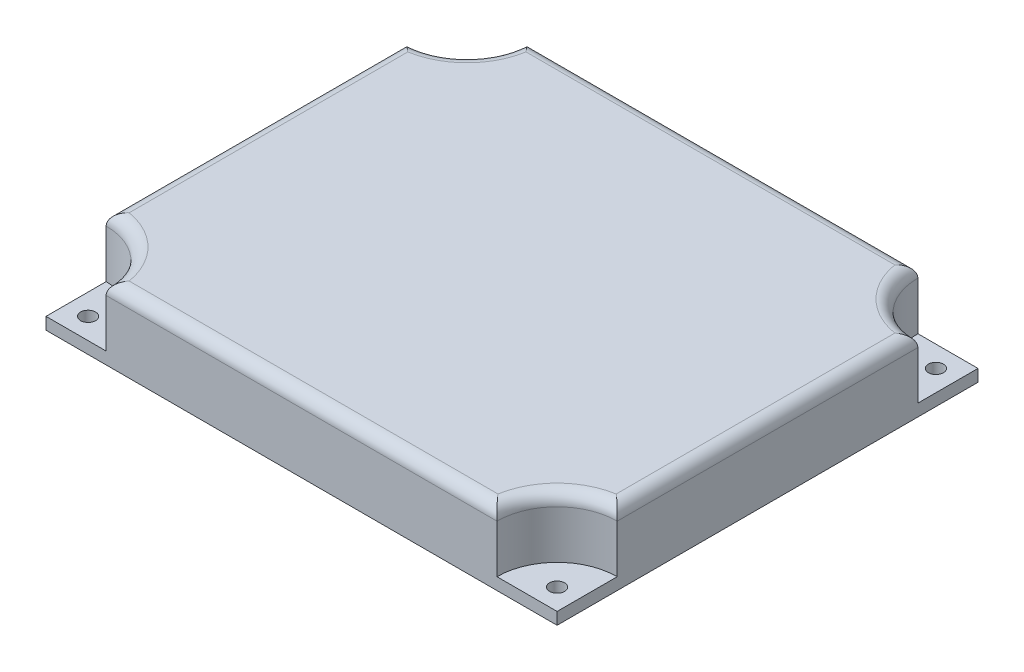
SolidWorks part; units mm, degrees
material "6061-T6 (SS)"
ref_plane "Front Plane" through (0, 0, 0) normal (0, 0, 1) x (1, 0, 0)
ref_plane "Top Plane" through (0, 0, 0) normal (0, 1, 0) x (1, 0, 0)
ref_plane "Right Plane" through (0, 0, 0) normal (1, 0, 0) x (0, 0, -1)
sketch "Sketch2" plane through (0, 0, 0) normal (0, 1, 0) x (1, 0, 0)
  line L1 (-42.5, -35) -> (42.5, -35)
  line L2 (-42.5, -35) -> (-42.5, 35)
  line L3 (-42.5, 35) -> (42.5, 35)
  line L4 (42.5, -35) -> (42.5, 35)
  line L5 (-42.5, -35) -> (42.5, 35) construction
  line L6 (-42.5, 35) -> (42.5, -35) construction
  point P0 (0, 0)
  dimension "D1" = 85
  dimension "D2" = 70
extrude "Boss-Extrude1" add sketch "Sketch2" along normal blind 12
sketch "Sketch3" plane through (0, 0, 0) normal (0, -1, 0) x (1, 0, 0)
  line L1 (-39, -39) -> (39, -39)
  line L2 (-39, -39) -> (-39, 39)
  line L3 (-39, 39) -> (39, 39)
  line L4 (39, -39) -> (39, 39)
  line L5 (-39, -39) -> (39, 39) construction
  line L6 (-39, 39) -> (39, -39) construction
  point P0 (0, 0)
  dimension "D1" = 78
  dimension "D2" = 78
extrude "Cut-Extrude1" [suppressed] cut sketch "Sketch3" against normal blind 10
ref_plane "Plane1" through (0, 0, 6) normal (0, 0, -1) x (-1, 0, 0)
ref_plane "Plane2" through (0, 0, 0) normal (1, 0, 0) x (0, 0, -1)
fillet "Fillet1" [suppressed] radius 2
sketch "Sketch4" plane through (0, 12, 0) normal (0, 1, 0) x (1, 0, 0)
  line L5 (0, 0) -> (43.0078, 0) construction
  circle A1 centre (42.5, -35) radius 10
  circle A2 centre (-42.5, -35) radius 10
  circle A3 centre (-42.5, 35) radius 10
  circle A4 centre (42.5, 35) radius 10
  dimension "D1" = 20
extrude "Cut-Extrude3" cut sketch "Sketch4" against normal blind 10 contours A1 | A2 | A3 | A4
sketch "Sketch5" plane through (0, 2, 0) normal (0, 1, 0) x (1, 0, 0)
  line L4 (-42.5, -25) -> (-42.5, -35) construction
  line L5 (-42.5, -35) -> (-32.5, -35) construction
  line L6 (42.5, -35) -> (42.5, -25) construction
  line L7 (32.5, -35) -> (42.5, -35) construction
  line L8 (32.5, 35) -> (42.5, 35) construction
  line L9 (42.5, 35) -> (42.5, 25) construction
  line L10 (-42.5, 35) -> (-32.5, 35) construction
  line L11 (-42.5, 25) -> (-42.5, 35) construction
  point P20 (-39, 31.5)
  point P21 (-39, -31.5)
  point P22 (39, -31.5)
  point P23 (39, 31.5)
  dimension "D1" = 3.5
  dimension "D2" = 3.5
  dimension "D3" = 3.5
  dimension "D4" = 3.5
  dimension "D5" = 3.5
  dimension "D6" = 3.5
  dimension "D7" = 3.5
  dimension "D8" = 3.5
sketch "Sketch8" plane through (0, 0, 0) normal (0, -1, 0) x (1, 0, 0)
  line L0 (-42.5, -35) -> (-42.5, 35) construction
  line L1 (-42.5, 35) -> (42.5, 35) construction
  line L3 (35.5, -25) -> (35.5, 25)
  line L4 (33.5, 27) -> (-33.5, 27)
  line L5 (-35.5, 25) -> (-35.5, -25)
  line L6 (-33.5, -27) -> (33.5, -27)
  arc A0 (35.5, 25) -> (33.5, 27) centre (33.5, 25) ccw
  arc A1 (-33.5, 27) -> (-35.5, 25) centre (-33.5, 25) ccw
  arc A2 (-35.5, -25) -> (-33.5, -27) centre (-33.5, -25) ccw
  arc A3 (35.5, -25) -> (33.5, -27) centre (33.5, -25) cw
  dimension "D1" = 2
  dimension "D2" = 54
  dimension "D3" = 71
  dimension "D4" = 7
  dimension "D5" = 8
fillet "Fillet2" radius 2 8 edges at (42.5, 12, 0) (35.4289, 12, 27.9289) (0, 12, 35) (-35.4289, 12, 27.9289) (-42.5, 12, 0) (-35.4289, 12, -27.9289) (0, 12, -35) (35.4289, 12, -27.9289)
hole_wizard "M3x0.5 Tapped Hole1" positions "Sketch9" profile "Sketch10" tap size "M3x0.5" standard "ANSI Metric"
sketch "Sketch9" plane through (0, 2, 0) normal (0, 1, 0) x (1, 0, 0)
  point P0 (-39, 31.5)
  point P3 (-39, -31.5)
  point P6 (39, -31.5)
  point P9 (39, 31.5)
sketch "Sketch10" plane through (-39, 2, -31.5) normal (1, 0, 0) x (0, 0, 1)
  line L0 (0, 0) -> (0, 10.7511)
  line L1 (0, 10.7511) -> (1.25, 10)
  line L2 (1.25, 10) -> (1.25, 0)
  line L5 (1.25, 0) -> (0, 0)
  line L10 (0, 10.7511) -> (-1.25, 10) construction
  line L11 (0, -6.35) -> (0, 107.95) construction
  dimension "Tap Drill Dia." = 2.5
  dimension "Tap Drill Depth" = 10
  dimension "Drill Angle" = 118
extrude "Cut-Extrude4" cut sketch "Sketch8" against normal blind 8
